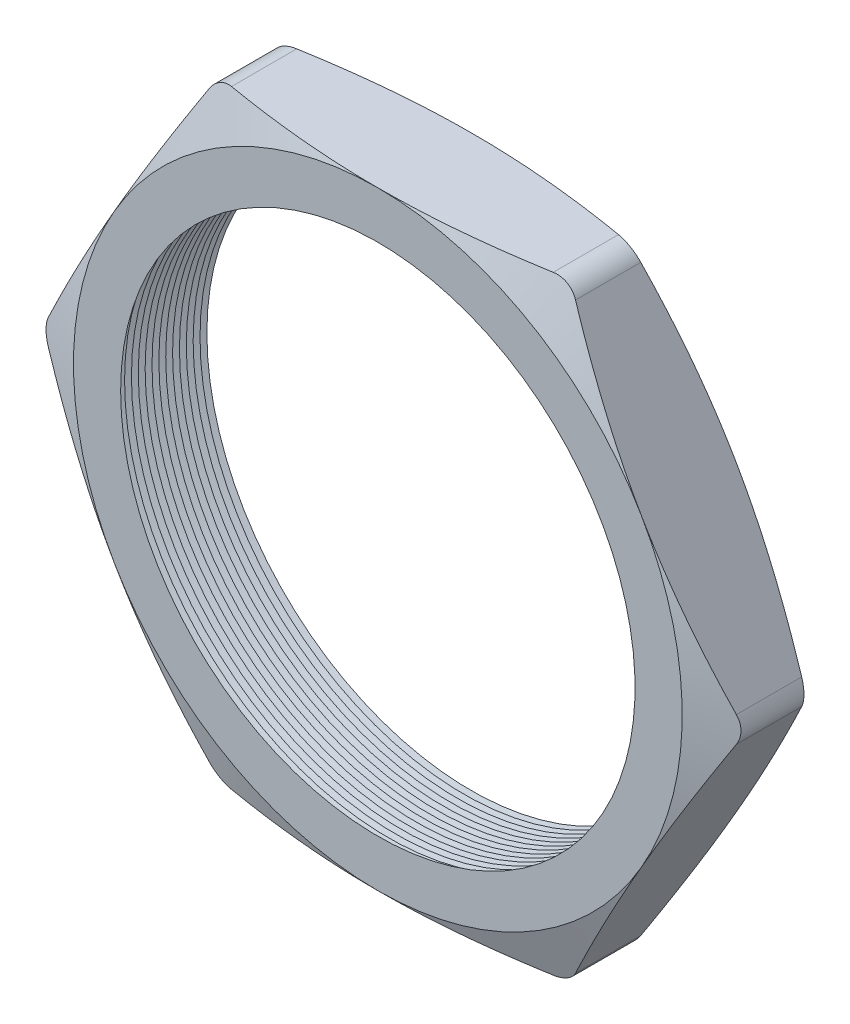
SolidWorks part; units mm, degrees
ref_plane "Front Plane" through (0, 0, 0) normal (0, 0, 1) x (1, 0, 0)
ref_plane "Top Plane" through (0, 0, 0) normal (0, 1, 0) x (1, 0, 0)
ref_plane "Right Plane" through (0, 0, 0) normal (1, 0, 0) x (0, 0, -1)
sketch "Sketch1" plane through (0, 0, 0) normal (0, 0, 1) x (1, 0, 0)
  line L1 (-10.4119, 0) -> (-5.206, -9.017)
  line L2 (-5.206, -9.017) -> (5.206, -9.017)
  line L3 (5.206, -9.017) -> (10.4119, 0)
  line L4 (10.4119, 0) -> (5.206, 9.017)
  line L5 (5.206, 9.017) -> (-5.206, 9.017)
  line L6 (-5.206, 9.017) -> (-10.4119, 0)
  circle A0 centre (0, 0) radius 9.017 construction
  circle A1 centre (0, 0) radius 7.62
  dimension "TS" = 15.24
  dimension "H" = 18.034
extrude "Extrude1" add sketch "Sketch1" along normal blind 2.794
fillet "Fillet1" radius 0.762 6 edges at (-5.206, 9.017, 1.397) (-10.4119, 0, 1.397) (-5.206, -9.017, 1.397) (5.206, -9.017, 1.397) (10.4119, 0, 1.397) (5.206, 9.017, 1.397)
sketch "Sketch2" plane through (0, 0, 2.794) normal (0, 0, 1) x (1, 0, 0)
  line L0 (4.766, 9.017) -> (-4.766, 9.017) construction
  circle A0 centre (0, 0) radius 9.017
extrude "Cut-Extrude1" cut sketch "Sketch2" against normal through all draft 70 flip side to cut
sketch "Sketch3" plane through (0, 0, 0) normal (0, 0, -1) x (-1, 0, 0)
  circle A0 centre (0, 0) radius 9.017
extrude "Cut-Extrude2" cut sketch "Sketch3" against normal through all draft 70 flip side to cut
sketch "Sketch4" plane through (0, 0, 0) normal (0, 1, 0) x (1, 0, 0)
  line L0 (-7.62, -2.794) -> (-7.62, -2.3541)
  line L2 (-7.62, -2.3541) -> (-8.001, -2.574)
  line L3 (-8.001, -2.574) -> (-7.62, -2.794)
  line L5 (-7.62, 0) -> (-7.62, -2.794) construction
  line L6 (-7.62, -2.794) -> (7.62, -2.794) construction
  dimension "D1" = 60
  dimension "D2" = 60
  dimension "D3" = 0.381
revolve "Cut-Revolve1" cut sketch "Sketch4" angle 360 about axis through (0, 0, 2.794) along (0, 0, -1)
pattern_linear "LPattern1" count 14 spacing 0.2032 along (0, 0, -1) of "Cut-Revolve1"
